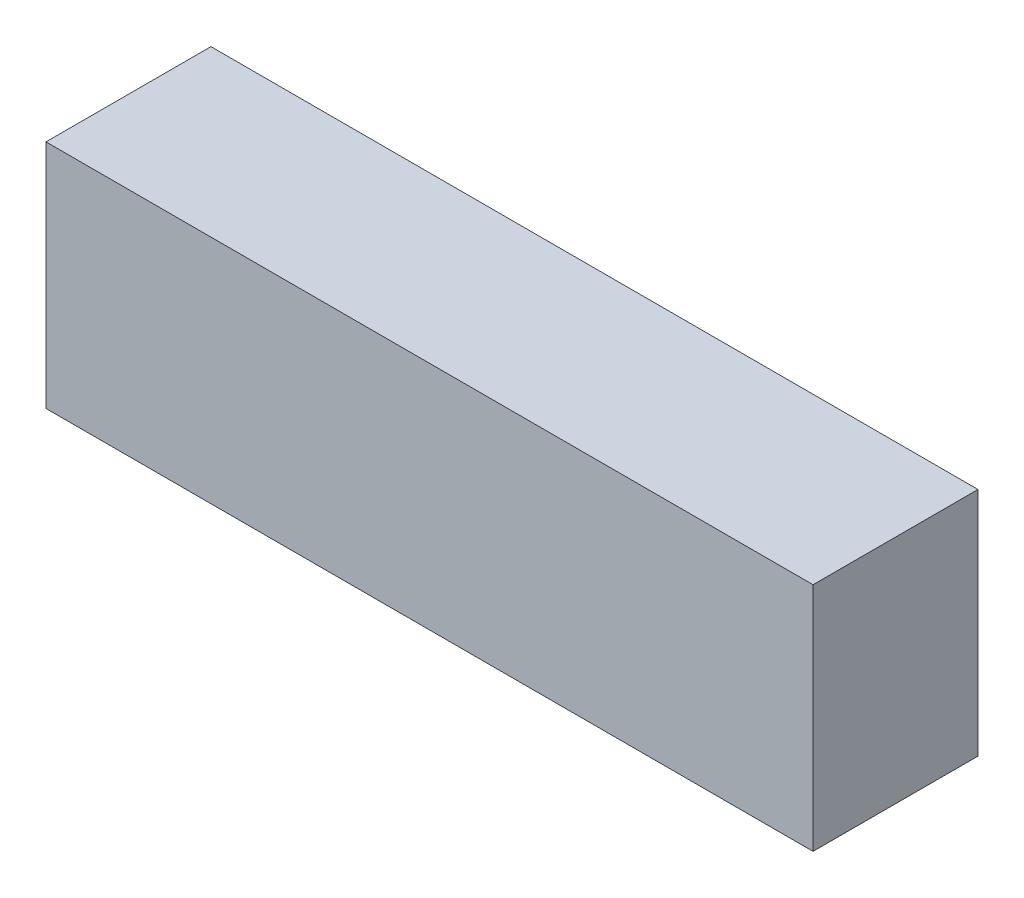
SolidWorks part; units mm, degrees
ref_plane "前视基准面" through (0, 0, 0) normal (0, 0, 1) x (1, 0, 0)
ref_plane "上视基准面" through (0, 0, 0) normal (0, 1, 0) x (1, 0, 0)
ref_plane "右视基准面" through (0, 0, 0) normal (1, 0, 0) x (0, 0, -1)
sketch "草图1" plane through (0, 0, 0) normal (0, 0, 1) x (1, 0, 0)
  line L1 (-46.5, 14) -> (46.5, 14)
  line L2 (-46.5, 14) -> (-46.5, -14)
  line L3 (-46.5, -14) -> (46.5, -14)
  line L4 (46.5, 14) -> (46.5, -14)
  line L5 (-46.5, 14) -> (46.5, -14) construction
  line L6 (-46.5, -14) -> (46.5, 14) construction
  point P1 (0, 0)
  dimension "D1" = 28
  dimension "D2" = 93
extrude "凸台-拉伸1" add sketch "草图1" along normal blind 20
